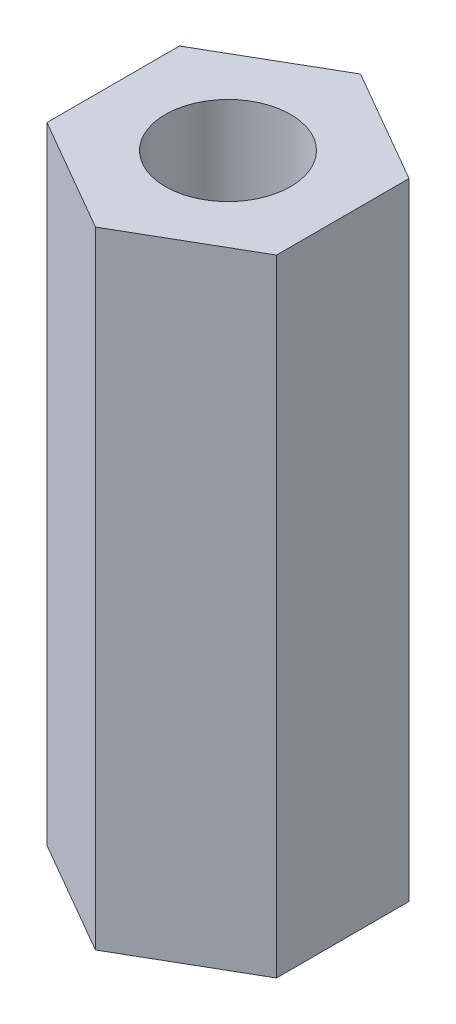
SolidWorks part; units mm, degrees
material "Простая углеродистая сталь"
ref_plane "Спереди" through (0, 0, 0) normal (0, 0, 1) x (1, 0, 0)
ref_plane "Сверху" through (0, 0, 0) normal (0, 1, 0) x (1, 0, 0)
ref_plane "Справа" through (0, 0, 0) normal (1, 0, 0) x (0, 0, -1)
sketch "Эскиз1" plane through (0, 0, 0) normal (0, 1, 0) x (1, 0, 0)
  line L0 (0, 3.1754) -> (0, 0) construction
  line L1 (0, 3.1754) -> (-2.75, 1.5877)
  line L2 (-2.75, 1.5877) -> (-2.75, -1.5877)
  line L3 (-2.75, -1.5877) -> (0, -3.1754)
  line L4 (0, -3.1754) -> (2.75, -1.5877)
  line L5 (2.75, -1.5877) -> (2.75, 1.5877)
  line L6 (2.75, 1.5877) -> (0, 3.1754)
  circle A0 centre (0, 0) radius 2.75 construction
  circle A1 centre (0, 0) radius 1.5
  dimension "D2" = 3
  dimension "D1" = 5.5
extrude "Бобышка-Вытянуть1" add sketch "Эскиз1" along normal blind 15
